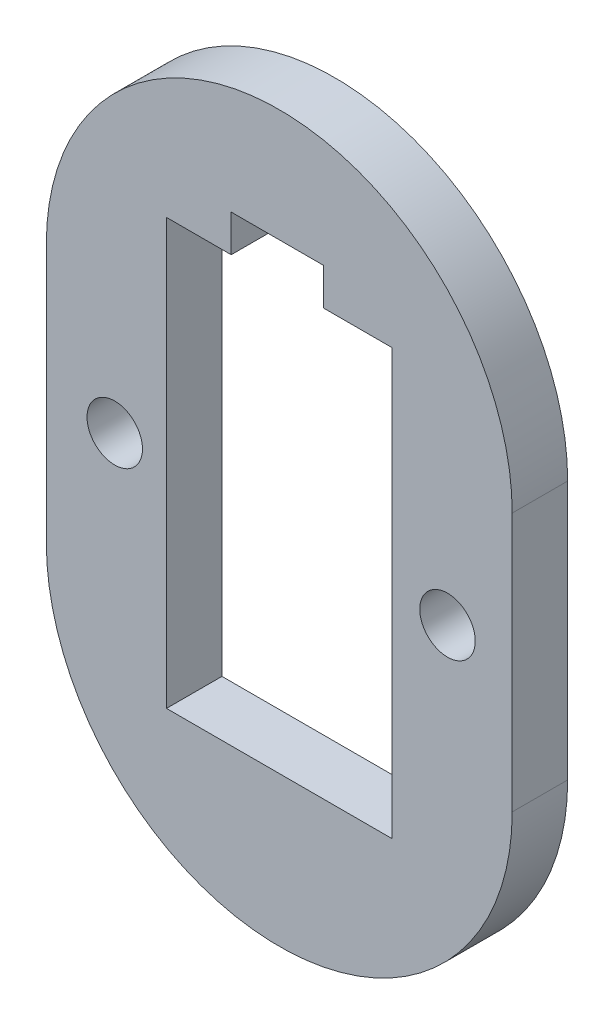
SolidWorks part; units mm, degrees
ref_plane "Front Plane" through (0, 0, 0) normal (0, 0, 1) x (1, 0, 0)
ref_plane "Top Plane" through (0, 0, 0) normal (0, 1, 0) x (1, 0, 0)
ref_plane "Right Plane" through (0, 0, 0) normal (1, 0, 0) x (0, 0, -1)
sketch "Model" plane through (0, 0, 0) normal (0, 0, 1) x (1, 0, 0)
  line L0 (19.5862, 6.709) -> (19.5862, 29.709)
  line L1 (10.8862, 29.709) -> (7.3862, 29.709)
  line L2 (10.8862, 31.709) -> (10.8862, 29.709)
  line L3 (15.8862, 31.709) -> (10.8862, 31.709)
  line L4 (15.8862, 29.709) -> (15.8862, 31.709)
  line L5 (19.5862, 29.709) -> (15.8862, 29.709)
  line L6 (0.8862, 25.209) -> (0.8862, 11.209)
  line L7 (26.0862, 11.209) -> (26.0862, 25.209)
  line L8 (7.3862, 6.709) -> (19.5862, 6.709)
  line L9 (7.3862, 29.709) -> (7.3862, 6.709)
  line L10 (0.8862, 18.209) -> (26.0862, 18.209) construction
  line L11 (13.4862, 37.809) -> (13.4862, -1.391) construction
  circle A0 centre (4.5863, 18.209) radius 1.5
  circle A1 centre (22.5863, 18.209) radius 1.5
  arc A2 (26.0862, 25.209) -> (0.8862, 25.209) centre (13.4862, 25.209) ccw
  arc A3 (0.8862, 11.209) -> (26.0862, 11.209) centre (13.4862, 11.209) ccw
  dimension "D1" = 18
  dimension "D2" = 12.2
extrude "Boss-Extrude1" add sketch "Model" along normal blind 3
